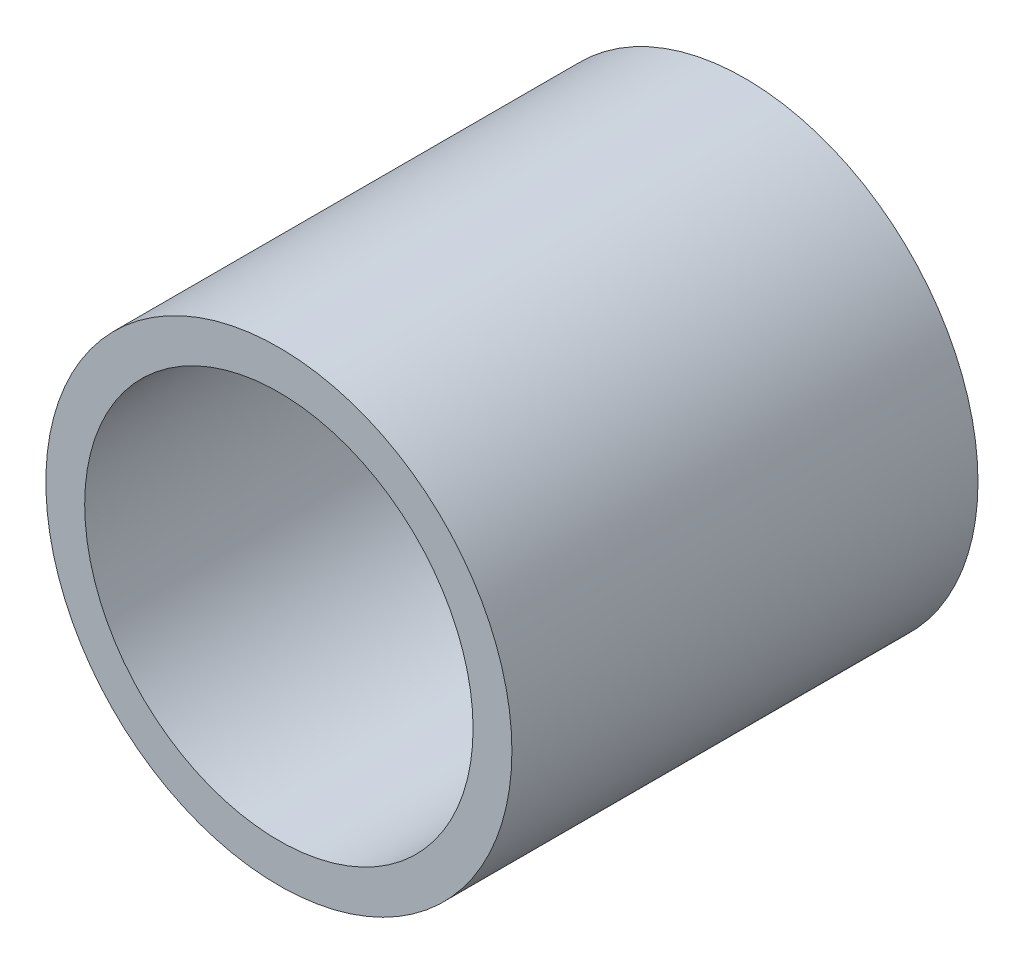
SolidWorks part; units mm, degrees
ref_plane "정면" through (0, 0, 0) normal (0, 0, 1) x (1, 0, 0)
ref_plane "윗면" through (0, 0, 0) normal (0, 1, 0) x (1, 0, 0)
ref_plane "우측면" through (0, 0, 0) normal (1, 0, 0) x (0, 0, -1)
sketch "스케치1" plane through (0, 0, 0) normal (0, 0, 1) x (1, 0, 0)
  circle A1 centre (0, 0) radius 12
  dimension "D1" = 24
extrude "보스-돌출1" add sketch "스케치1" along normal blind 4
ref_plane "평면1" through (0, 0, 4) normal (0, 0, 1) x (1, 0, 0)
sketch "스케치2" plane through (0, 0, 4) normal (0, 0, 1) x (1, 0, 0)
  circle A0 centre (0, 0) radius 12
  circle A1 centre (0, 0) radius 10
  dimension "D1" = 20
  dimension "D2" = 24
extrude "보스-돌출2" add sketch "스케치2" along normal blind 20
ref_plane "평면3" through (0, 0, 0) normal (0, 0, -1) x (-1, 0, 0)
sketch "스케치4" plane through (0, 0, 0) normal (0, 0, -1) x (-1, 0, 0)
  circle A0 centre (0, 0) radius 1.5
extrude "컷-돌출1" cut sketch "스케치4" against normal through all
ref_plane "평면4" through (0, 0, 0) normal (0, 0, -1) x (-1, 0, 0)
sketch "스케치6" plane through (0, 0, 0) normal (0, 0, -1) x (-1, 0, 0)
  circle A0 centre (0, 0) radius 2.5
extrude "컷-돌출2" cut sketch "스케치6" against normal blind 3.5
ref_plane "평면5" through (0, 0, 0) normal (0, 0, -1) x (-1, 0, 0)
sketch "스케치7" plane through (0, 0, 0) normal (0, 0, -1) x (-1, 0, 0)
  line L0 (-12, 0) -> (12, 0) construction
  line L2 (0, 12) -> (0, -12) construction
  circle A0 centre (0, 0) radius 12 construction
  circle A1 centre (-5, 0) radius 1
  circle A8 centre (5, 0) radius 1
  point P23 (19, 0)
  point P24 (-19, 0)
  point P25 (0, 5)
  point P26 (0, -5)
  dimension "D8" = 2
  dimension "D1" = 5
  dimension "D11" = 38
  dimension "D12" = 5
extrude "컷-돌출3" cut sketch "스케치7" against normal through all
